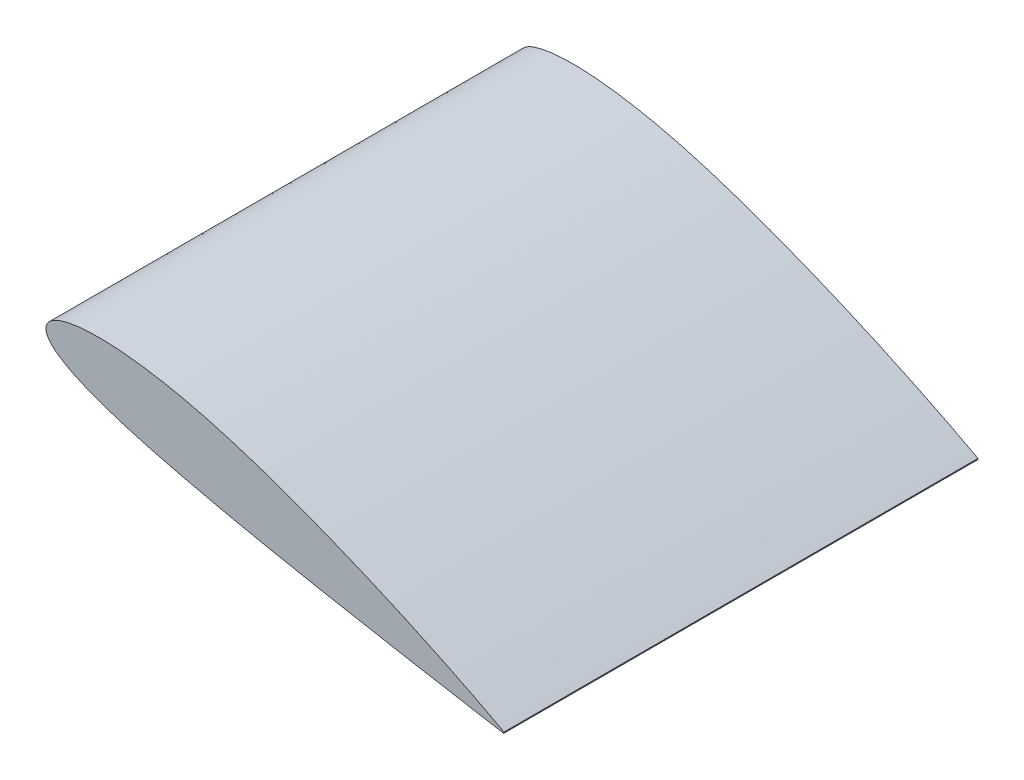
SolidWorks part; units mm, degrees
ref_plane "Front Plane"
ref_plane "Top Plane" through (0, 0, 0) normal (0, 1, 0) x (1, 0, 0)
ref_plane "Right Plane" through (0, 0, 0) normal (1, 0, 0) x (0, 0, -1)
curve "Krzywa1"
  spline degree 3 poles (1, 0.0015, 0) (0.9991, 0.0017, 0) (0.9956, 0.0025, 0) (0.9875, 0.0044, 0) (0.9742, 0.0074, 0) (0.9556, 0.0115, 0) (0.9322, 0.0166, 0) (0.904, 0.0224, 0) (0.8713, 0.0289, 0) (0.8346, 0.0358, 0) (0.7942, 0.043, 0) (0.7505, 0.0503, 0) (0.7041, 0.0574, 0) (0.6553, 0.0643, 0) (0.6048, 0.0707, 0) (0.5531, 0.0765, 0) (0.5007, 0.0814, 0) (0.4483, 0.0853, 0) (0.3962, 0.0881, 0) (0.3451, 0.0894, 0) (0.2956, 0.089, 0) (0.2483, 0.0868, 0) (0.2039, 0.083, 0) (0.1628, 0.0776, 0) (0.1256, 0.0708, 0) (0.0927, 0.0627, 0) (0.0643, 0.0537, 0) (0.0409, 0.0439, 0) (0.0225, 0.0337, 0) (0.0093, 0.0231, 0) (0.0011, 0.0119, 0) (-0.001, -0.0001, 0) (0.0034, -0.0114, 0) (0.0135, -0.0208, 0) (0.0284, -0.0287, 0) (0.0479, -0.0355, 0) (0.0722, -0.0411, 0) (0.1009, -0.0456, 0) (0.1337, -0.0489, 0) (0.1703, -0.0511, 0) (0.2104, -0.0521, 0) (0.2535, -0.0522, 0) (0.2992, -0.0514, 0) (0.347, -0.0499, 0) (0.3967, -0.0479, 0) (0.4476, -0.0455, 0) (0.4993, -0.0424, 0) (0.5511, -0.0389, 0) (0.6024, -0.0352, 0) (0.6526, -0.0314, 0) (0.7012, -0.0275, 0) (0.7477, -0.0237, 0) (0.7915, -0.0201, 0) (0.8321, -0.0166, 0) (0.8691, -0.0134, 0) (0.9021, -0.0105, 0) (0.9307, -0.0079, 0) (0.9546, -0.0057, 0) (0.9734, -0.004, 0) (0.9871, -0.0027, 0) (0.9953, -0.0019, 0) (0.999, -0.0016, 0) (1, -0.0015, 0) knots 0 0 0 0 0.001308 0.005358 0.012063 0.021337 0.033087 0.047171 0.063441 0.081714 0.101785 0.123442 0.146433 0.170517 0.195424 0.220875 0.246594 0.272302 0.297725 0.322799 0.347029 0.370162 0.391954 0.412188 0.43067 0.447231 0.461732 0.474085 0.484276 0.492392 0.498749 0.5041 0.509453 0.51579 0.523838 0.533885 0.546005 0.560171 0.576284 0.594211 0.613803 0.634869 0.65721 0.680611 0.704835 0.729853 0.755197 0.780583 0.805729 0.830359 0.854204 0.877002 0.898494 0.918443 0.936623 0.952826 0.966868 0.978592 0.987852 0.994547 0.998596 1 1 1 1
sketch "Szkic1" plane through (0, 0, 0) normal (0, 0, 1) x (1, 0, 0)
  line L0 (483.1531, -128.6996) -> (482.7727, -130.1195)
  spline S1 degree 3 poles (483.1531, -128.6996) (482.7604, -128.485) (481.1522, -127.6063) (477.4975, -125.6911) (471.4413, -122.4897) (463.0266, -118.1151) (452.3451, -112.63) (433.8974, -103.3494) (406.1029, -89.8366) (367.7929, -72.1633) (332.0969, -56.716) (301.2435, -44.1204) (277.0088, -34.6446) (252.3541, -25.502) (227.5425, -16.8217) (202.7658, -8.7238) (178.2516, -1.4774) (154.2602, 4.7246) (131.1529, 9.8003) (109.2031, 13.6939) (88.678, 16.4038) (69.8233, 17.9149) (52.8715, 18.2988) (38.0243, 17.6023) (25.4461, 15.9279) (15.2449, 13.3534) (7.4769, 9.9398) (2.0801, 5.6034) (-0.5172, 0.0835) (0.1817, -5.9653) (3.849, -11.794) (9.9851, -17.5326) (18.5639, -23.3461) (29.5378, -29.2084) (42.8083, -35.0794) (58.2303, -40.9271) (75.6437, -46.7075) (94.857, -52.404) (115.6609, -58.0206) (137.8328, -63.5493) (161.1297, -69.0182) (185.3701, -74.4696) (210.3006, -79.8784) (235.6791, -85.0898) (261.1392, -90.1153) (294.393, -96.5094) (334.0448, -103.8664) (371.9755, -110.7535) (405.182, -116.6776) (428.2103, -120.7496) (448.4807, -124.2625) (460.2857, -126.3009) (469.6184, -127.8902) (476.3628, -129.0398) (480.4622, -129.7177) (482.2995, -130.0372) (482.7727, -130.1195) knots 0 0 0 0 0.001308 0.005358 0.012063 0.021337 0.033087 0.047171 0.081714 0.123442 0.170517 0.195424 0.220875 0.246594 0.272302 0.297725 0.322799 0.347029 0.370162 0.391954 0.412188 0.43067 0.447231 0.461732 0.474085 0.484276 0.492392 0.498749 0.5041 0.509453 0.51579 0.523838 0.533885 0.546005 0.560171 0.576284 0.594211 0.613803 0.634869 0.65721 0.680611 0.704835 0.729853 0.755197 0.780583 0.805729 0.854204 0.898494 0.918443 0.952826 0.966868 0.978592 0.987852 0.994547 0.998596 1 1 1 1
extrude "Dodanie-wyciągnięcie1" add sketch "Szkic1" along normal blind 500
